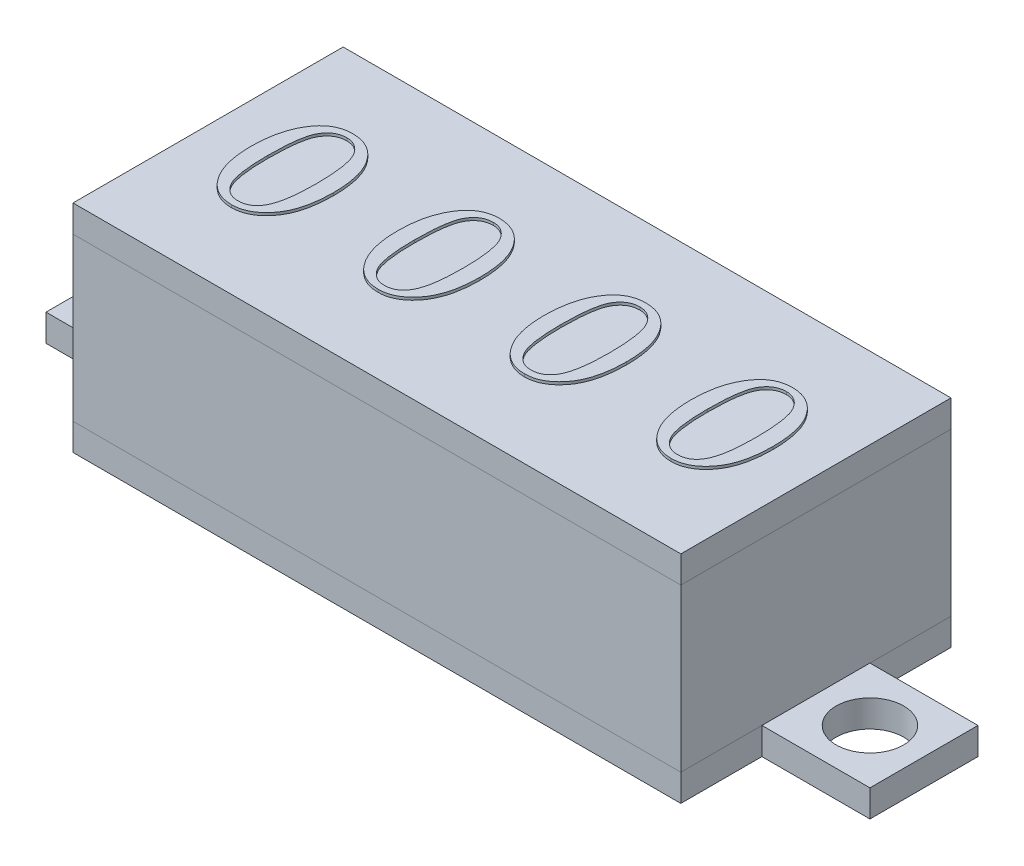
SolidWorks part; units mm, degrees
ref_plane "Front Plane" through (0, 0, 0) normal (0, 0, 1) x (1, 0, 0)
ref_plane "Top Plane" through (0, 0, 0) normal (0, 1, 0) x (1, 0, 0)
ref_plane "Right Plane" through (0, 0, 0) normal (1, 0, 0) x (0, 0, -1)
sketch "Sketch1" plane through (0, 0, 0) normal (0, 1, 0) x (1, 0, 0)
  line L1 (-12.4387, 4.7335) -> (10.0613, 4.7335)
  line L2 (-12.4387, 4.7335) -> (-12.4387, -5.2665)
  line L3 (-12.4387, -5.2665) -> (10.0613, -5.2665)
  line L4 (10.0613, 4.7335) -> (10.0613, -5.2665)
  dimension "D1" = 22.5
  dimension "D2" = 10
extrude "Boss-Extrude1" add sketch "Sketch1" along normal blind 6
sketch "Sketch2" plane through (0, 0, 0) normal (0, -1, 0) x (1, 0, 0)
  line L0 (10.0613, -1.7335) -> (10.0613, 2.2665)
  line L1 (10.0613, -4.7335) -> (-12.4387, -4.7335)
  line L2 (10.0613, -4.7335) -> (10.0613, 5.2665)
  line L3 (10.0613, 5.2665) -> (-12.4387, 5.2665)
  line L4 (-12.4387, -4.7335) -> (-12.4387, 5.2665)
  line L5 (10.0613, 2.2665) -> (14.0613, 2.2665)
  line L7 (10.0613, -1.7335) -> (14.0613, -1.7335)
  line L8 (14.0613, 2.2665) -> (14.0613, -1.7335)
  line L9 (12.0613, -1.7335) -> (12.0613, 2.2665) construction
  line L10 (14.0613, 0.2665) -> (10.0613, 0.2665) construction
  line L11 (-12.4387, 2.2665) -> (-16.4387, 2.2665)
  line L13 (-12.4387, -1.7335) -> (-16.4387, -1.7335)
  line L14 (-16.4387, 2.2665) -> (-16.4387, -1.7335)
  line L15 (-12.4387, 0.2665) -> (-16.4387, -1.7335) construction
  line L16 (-12.4387, 0.2665) -> (-16.4387, 2.2665) construction
  line L17 (-12.4387, -1.7335) -> (-12.4387, 2.2665)
  circle A0 centre (12.0613, 0.2665) radius 1.25
  circle A1 centre (-14.4387, 0.2665) radius 1.25
  point P6 (10.0613, 0.2665)
  point P11 (-12.4387, 0.2665)
  line M19 (-12.4387, 5.2665) -> (-12.4387, -4.7335)
  line M20 (-12.4387, -4.7335) -> (10.0613, -4.7335)
  line M21 (10.0613, -4.7335) -> (10.0613, 5.2665)
  line M22 (10.0613, 5.2665) -> (-12.4387, 5.2665)
  dimension "D7" = 2.5
  dimension "D8" = 2.5
  dimension "D1" = 4
  dimension "D2" = 4
  dimension "D3" = 4
  dimension "D4" = 4
  dimension "D5" = 3
  dimension "D6" = 3
extrude "Boss-Extrude2" add sketch "Sketch2" along normal blind 1 separate body contours L8 L5 L7 A0 M21 | L4 M22 M19 M20 M21 | L11 L14 L13 L4 A1
sketch "Sketch3" plane through (0, 6, 0) normal (0, 1, 0) x (1, 0, 0)
  line L4 (-12.4387, 4.7335) -> (-12.4387, -5.2665)
  line L5 (-12.4387, -5.2665) -> (10.0613, -5.2665)
  line L6 (10.0613, -5.2665) -> (10.0613, 4.7335)
  line L7 (10.0613, 4.7335) -> (-12.4387, 4.7335)
  line L8 (-12.4387, 4.7335) -> (-12.4387, -5.2665)
  line L9 (-12.4387, -5.2665) -> (10.0613, -5.2665)
  line L10 (10.0613, -5.2665) -> (10.0613, 4.7335)
  line L11 (10.0613, 4.7335) -> (-12.4387, 4.7335)
  dimension "D1" = 0
extrude "Boss-Extrude3" add sketch "Sketch3" along normal blind 1 separate body
sketch "Sketch4" plane through (0, 7, 0) normal (0, 1, 0) x (1, 0, 0)
  text T0 "0 0 0 0" font "Century Schoolbook" height in points 18
extrude "Boss-Extrude4" add sketch "Sketch4" along normal blind 0.1
